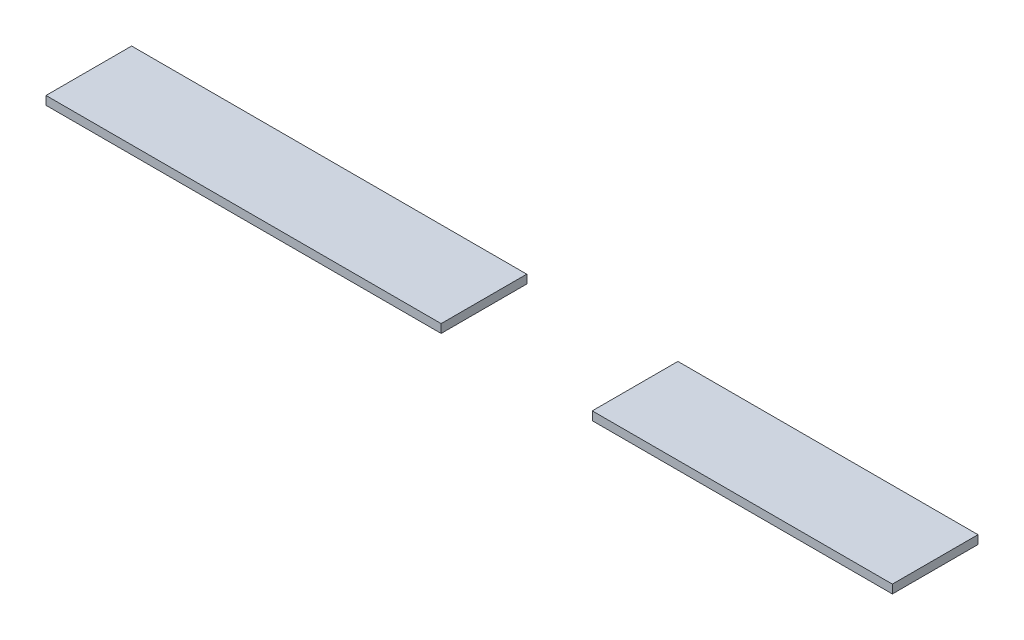
SolidWorks part; units mm, degrees
ref_plane "Front Plane" through (0, 0, 0) normal (0, 0, 1) x (1, 0, 0)
ref_plane "Top Plane" through (0, 0, 0) normal (0, 1, 0) x (1, 0, 0)
ref_plane "Right Plane" through (0, 0, 0) normal (1, 0, 0) x (0, 0, -1)
sketch "Sketch1" plane through (0, 0, 0) normal (0, 1, 0) x (1, 0, 0)
  line L1 (-72.4372, 7.5221) -> (125.2628, 7.5221)
  line L2 (-72.4372, 7.5221) -> (-72.4372, -12.4779)
  line L3 (-72.4372, -12.4779) -> (125.2628, -12.4779)
  line L4 (125.2628, 7.5221) -> (125.2628, -12.4779)
  dimension "D1" = 197.7
  dimension "D2" = 20
extrude "Boss-Extrude1" add sketch "Sketch1" along normal blind 2
sketch "Sketch3" plane through (0, 0, 0) normal (0, -1, 0) x (-1, 0, 0)
  line L0 (-50.1628, -12.4779) -> (-50.1628, 7.5221)
  line L1 (72.4372, -12.4779) -> (-125.2628, -12.4779) construction
  line L2 (-125.2628, 7.5221) -> (72.4372, 7.5221) construction
  line L3 (-24.8628, -12.4779) -> (-24.8628, 7.5221)
  line L4 (-125.2628, -12.4779) -> (-125.2628, 7.5221) construction
  line L5 (72.4372, 7.5221) -> (72.4372, -12.4779) construction
  line L6 (-24.8628, -12.4779) -> (-50.1628, -12.4779)
  line L7 (-24.8628, 7.5221) -> (-50.1628, 7.5221)
  point P12 (72.4372, -2.4779)
  dimension "D1" = 75.1
  dimension "D2" = 97.3
extrude "Cut-Extrude2" cut sketch "Sketch3" against normal blind 10
sketch "Sketch4" plane through (0, 0, 0) normal (0, -1, 0) x (-1, 0, 0)
  line L0 (-24.8628, 7.5221) -> (72.4372, 7.5221) construction
  line L1 (-24.8628, -12.4779) -> (-19.8628, -12.4779)
  line L2 (-24.8628, -12.4779) -> (-24.8628, 7.5221)
  line L3 (-24.8628, 7.5221) -> (-19.8628, 7.5221)
  line L4 (-19.8628, -12.4779) -> (-19.8628, 7.5221)
  line L5 (-125.2628, 7.5221) -> (-50.1628, 7.5221) construction
  line L6 (-50.1628, -12.4779) -> (-55.1628, -12.4779)
  line L7 (-50.1628, -12.4779) -> (-50.1628, 7.5221)
  line L8 (-50.1628, 7.5221) -> (-55.1628, 7.5221)
  line L9 (-55.1628, -12.4779) -> (-55.1628, 7.5221)
  dimension "D1" = 5
  dimension "D2" = 5
extrude "Cut-Extrude3" cut sketch "Sketch4" against normal blind 10
